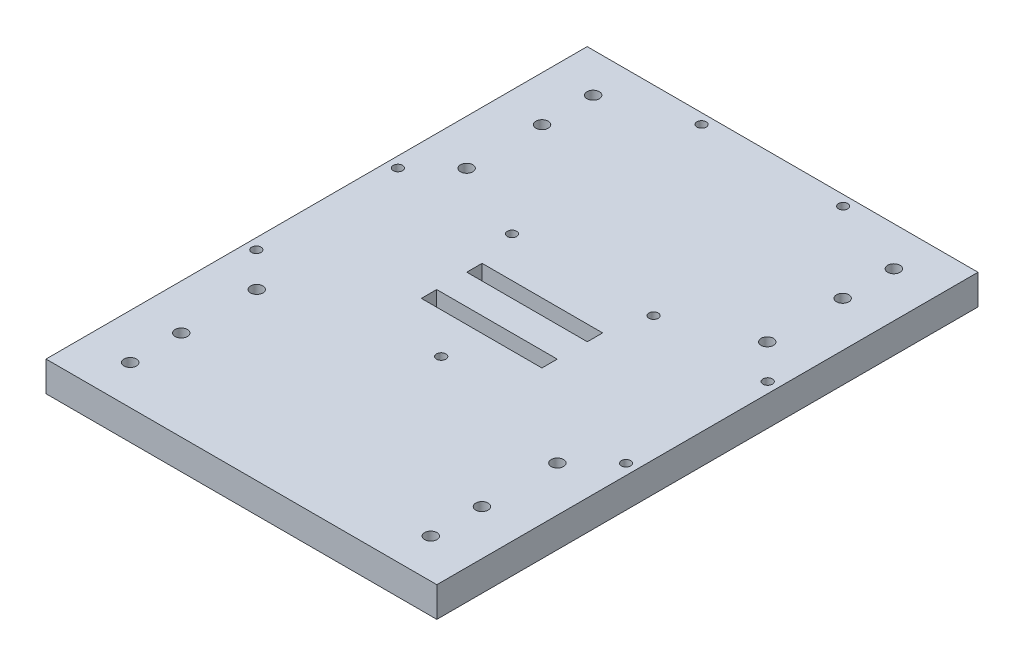
SolidWorks part; units mm, degrees
material "Carbon Sandwich"
ref_plane "Front Plane" through (0, 0, 0) normal (0, 0, 1) x (1, 0, 0)
ref_plane "Top Plane" through (0, 0, 0) normal (0, 1, 0) x (1, 0, 0)
ref_plane "Right Plane" through (0, 0, 0) normal (1, 0, 0) x (0, 0, -1)
sketch "Sketch1" plane through (0, 0, 0) normal (0, 1, 0) x (1, 0, 0)
  line L1 (0, 0) -> (0, 90)
  line L2 (0, 90) -> (-65, 90)
  line L11 (0, 0) -> (-65, 0)
  line L13 (-65, 90) -> (-65, 0)
  circle A3 centre (-50, 77) radius 2.05
  circle A5 centre (-50, 34.9) radius 2.05
  circle A6 centre (-50, 60) radius 2.05
  point P7 (-47.95, 77)
  dimension "D14" = 4.1
  dimension "D17" = 4.1
  dimension "D2" = 4.1
  dimension "D3" = 17
  dimension "D4" = 25.1
  dimension "D5" = 15
  dimension "D6" = 65
  dimension "D7" = 90
  dimension "D8" = 13
extrude "Boss-Extrude1" add sketch "Sketch1" along normal blind 10
mirror "Mirror1" of "Boss-Extrude1"
mirror "Mirror2" of "Mirror1", "Boss-Extrude1"
sketch "Sketch2" plane through (0, 10, 0) normal (0, 1, 0) x (1, 0, 0)
  line L0 (-20.05, 5) -> (20.05, 5)
  line L1 (-20.05, -5) -> (20.05, -5)
  line L2 (0, 5) -> (0, -5) construction
  line L3 (-20.05, -5) -> (-20.05, -10.1)
  line L4 (-20.05, -10.1) -> (20.05, -10.1)
  line L5 (20.05, -10.1) -> (20.05, -5)
  line L6 (20.05, 5) -> (20.05, 10.1)
  line L7 (20.05, 10.1) -> (-20.05, 10.1)
  line L8 (-20.05, 10.1) -> (-20.05, 5)
  point P10 (0, 0)
  dimension "D1" = 0
  dimension "D2" = 0
  dimension "D3" = 10
  dimension "D4" = 5.1
  dimension "D5" = 40.1
extrude "Cut-Extrude1" cut sketch "Sketch2" against normal blind 10
sketch "Sketch3" plane through (0, 10, 0) normal (0, 1, 0) x (1, 0, 0)
  circle A0 centre (-23.55, 86.6) radius 1.55
  circle A1 centre (-23.55, 23.55) radius 1.55
  circle A2 centre (-61.5, 23.55) radius 1.55
  circle A3 centre (23.55, 23.55) radius 1.55
  circle A4 centre (23.55, 86.6) radius 1.55
  circle A5 centre (61.5, 23.55) radius 1.55
  circle A6 centre (-61.5, -23.55) radius 1.55
  circle A7 centre (0, -23.55) radius 1.55
  circle A8 centre (61.5, -23.55) radius 1.55
  circle A9 centre (-23.55, 86.6) radius 1.55 construction
  circle A10 centre (-23.55, 23.55) radius 1.55 construction
  circle A11 centre (-61.5, 23.55) radius 1.55 construction
  circle A12 centre (23.55, 23.55) radius 1.55 construction
  circle A13 centre (61.5, 23.55) radius 1.55 construction
  circle A14 centre (23.55, 86.6) radius 1.55 construction
  circle A15 centre (0, -23.55) radius 1.55 construction
  circle A16 centre (-61.5, -23.55) radius 1.55 construction
  circle A17 centre (61.5, -23.55) radius 1.55 construction
extrude "Cut-Extrude2" cut sketch "Sketch3" against normal up to surface (10 mm away) up to face at (0, 0, -7.55)
